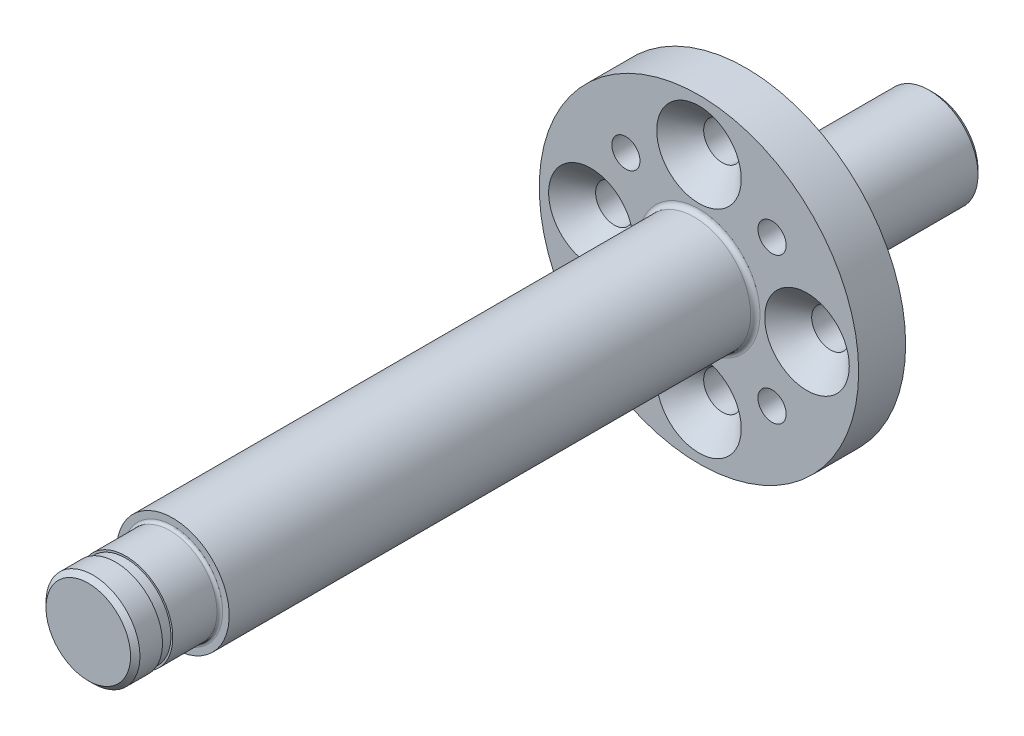
SolidWorks part; units mm, degrees
material "6063-T6"
ref_plane "Front Plane" through (0, 0, 0) normal (0, 0, 1) x (1, 0, 0)
ref_plane "Top Plane" through (0, 0, 0) normal (0, 1, 0) x (1, 0, 0)
ref_plane "Right Plane" through (0, 0, 0) normal (1, 0, 0) x (0, 0, -1)
sketch "Sketch1" plane through (0, 0, 0) normal (0, 0, 1) x (1, 0, 0)
  circle A0 centre (0, 0) radius 17
  dimension "D1" = 34
extrude "Boss-Extrude1" add sketch "Sketch1" along normal blind 5
sketch "Sketch3" plane through (0, 0, 0) normal (0, 0, -1) x (-1, 0, 0)
  circle A0 centre (0, 0) radius 5.2
  dimension "D1" = 10.4
extrude "Boss-Extrude3" add sketch "Sketch3" along normal blind 20
hole_wizard "CSK for M4 Hex Socket Countersunk Cap Screw1" positions "Sketch4" profile "Sketch5" countersink size "M4" standard "ISO" end condition through all
sketch "Sketch4" plane through (0, 0, 5) normal (0, 0, 1) x (1, 0, 0)
  circle A0 centre (0, 0) radius 11.5 construction
  circle A1 centre (0, 0) radius 17 construction
  point P0 (0, 11.5)
  point P7 (11.5, 0)
  point P9 (0, -11.5)
  point P11 (-11.5, 0)
  dimension "D1" = 23
sketch "Sketch5" plane through (0, 11.5, 5) normal (1, 0, 0) x (0, -1, 0)
  line L0 (0, 0) -> (0, 25)
  line L1 (0, 25) -> (2, 25)
  line L2 (2, 25) -> (2, 2.5)
  line L3 (2, 2.5) -> (4.5, 0)
  line L5 (4.5, 0) -> (0, 0)
  line L6 (-2, 2.5) -> (-4.5, 0) construction
  line L11 (0, -6.35) -> (0, 107.95) construction
  dimension "Thru Hole Dia." = 4
  dimension "Thru Hole Depth" = 25
  dimension "Near C'Sink Dia." = 9
  dimension "Near C'Sink Angle" = 90
hole_wizard "M4 Tapped Hole1" positions "Sketch6" profile "Sketch8" tap size "M4" standard "ISO" end condition through all
sketch "Sketch6" plane through (0, 0, 5) normal (0, 0, 1) x (1, 0, 0)
  line L0 (-11, 0) -> (11, 0) construction
  line L2 (-7.7782, -7.7782) -> (7.7782, 7.7782) construction
  line L3 (-7.7782, 7.7782) -> (7.7782, -7.7782) construction
  circle A0 centre (0, 0) radius 11 construction
  point P0 (7.7782, 7.7782)
  point P11 (-7.7782, -7.7782)
  point P16 (-7.7782, 7.7782)
  point P17 (7.7782, -7.7782)
  dimension "D1" = 22
  dimension "D2" = 45
cosmetic thread "Hole Thread1" parameters "D2"=4
cosmetic thread "Hole Thread2" parameters "D2"=4
cosmetic thread "Hole Thread3" parameters "D2"=4
cosmetic thread "Hole Thread4" parameters "D2"=4
sketch "Sketch8" plane through (7.7782, 7.7782, 5) normal (1, 0, 0) x (0, -1, 0)
  line L0 (0, 0) -> (0, 25)
  line L1 (0, 25) -> (1.5, 25)
  line L2 (1.5, 25) -> (1.5, 0)
  line L5 (1.5, 0) -> (0, 0)
  line L11 (0, -6.35) -> (0, 107.95) construction
  dimension "Thru Tap Drill Dia." = 3
  dimension "Thru Tap Drill Depth" = 25
ref_axis "Axis1" through (0, 0, -20) along (0, 0, 1)
sketch "Sketch10" plane through (0, 0, 0) normal (1, 0, 0) x (0, 0, -1)
  line L0 (-5, 0) -> (-5, 6)
  line L1 (-5, 17) -> (-5, -17) construction
  line L2 (-5, 6) -> (-61, 6)
  line L3 (-61, 6) -> (-61, 5)
  line L4 (-61, 5) -> (-66, 5)
  line L5 (-66, 5) -> (-66, 4.8)
  line L6 (-66, 4.8) -> (-67.1, 4.8)
  line L7 (-67.1, 4.8) -> (-67.1, 5)
  line L8 (-67.1, 5) -> (-70, 5)
  line L9 (-70, 5) -> (-70, 0)
  line L10 (20, 0) -> (-87.5828, 0) construction
  line L11 (-5, 0) -> (-70, 0)
  dimension "D1" = 6
  dimension "D2" = 5
  dimension "D3" = 5
  dimension "D4" = 4.8
  dimension "D5" = 1.1
  dimension "D6" = 2.9
  dimension "D7" = 56
revolve "Revolve1" add sketch "Sketch10" angle 360 about axis through (0, 0, -20) along (0, 0, 1)
chamfer "Chamfer1" distance 0.5 angle 45 2 edges at (-5, 0, 70) (-5.2, 0, -20)
fillet "Fillet1" radius 0.3 1 edges at (-5, 0, 61)
fillet "Fillet2" radius 0.5 2 edges at (-5.2, 0, 0) (-6, 0, 5)
